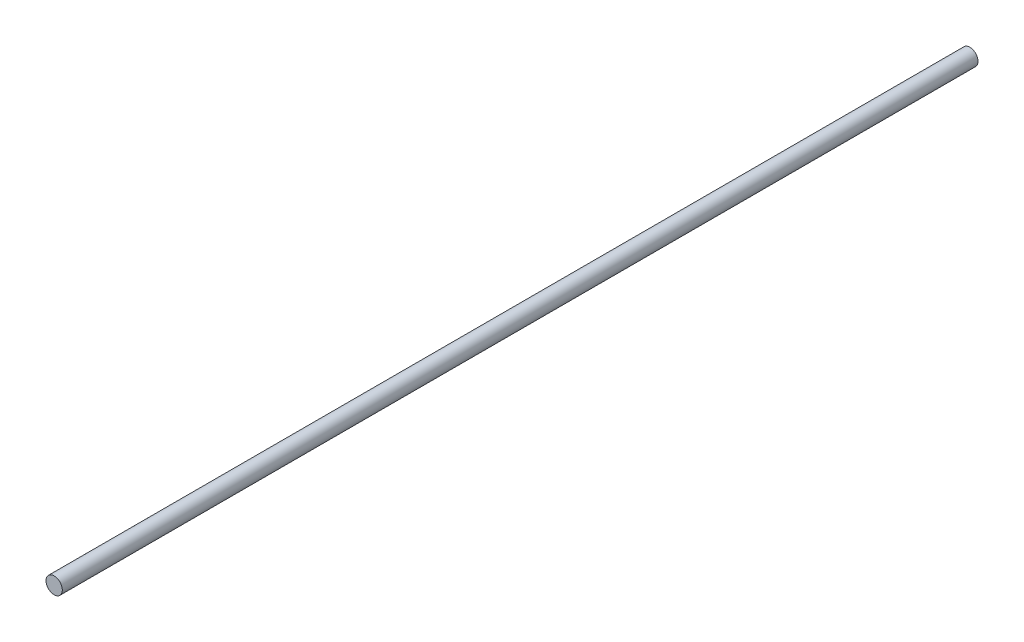
SolidWorks part; units mm, degrees
ref_plane "Front Plane" through (0, 0, 0) normal (0, 0, 1) x (1, 0, 0)
ref_plane "Top Plane" through (0, 0, 0) normal (0, 1, 0) x (1, 0, 0)
ref_plane "Right Plane" through (0, 0, 0) normal (1, 0, 0) x (0, 0, -1)
sketch "Sketch1" plane through (0, 0, 0) normal (0, 0, 1) x (1, 0, 0)
  circle A0 centre (0, 0) radius 3.175
  dimension "D1" = 6.35
extrude "Boss-Extrude1" add sketch "Sketch1" along normal blind 356
